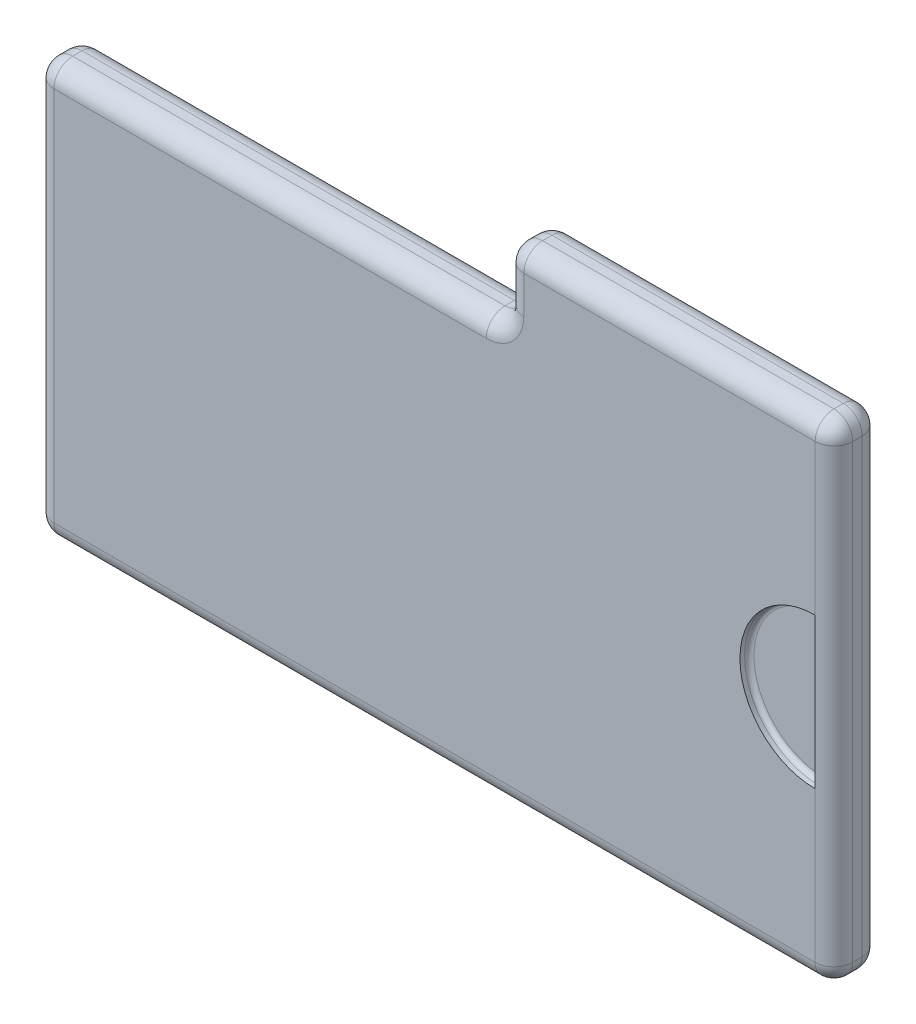
SolidWorks part; units mm, degrees
ref_plane "Alzado" through (0, 0, 0) normal (0, 0, 1) x (1, 0, 0)
ref_plane "Planta" through (0, 0, 0) normal (0, 1, 0) x (1, 0, 0)
ref_plane "Vista lateral" through (0, 0, 0) normal (1, 0, 0) x (0, 0, -1)
sketch "Croquis1" plane through (0, 0, 0) normal (0, 0, 1) x (1, 0, 0)
  line L0 (7.5, 26) -> (42.5, 26)
  line L2 (-42.5, 18) -> (-42.5, -26)
  line L3 (-42.5, -26) -> (42.5, -26)
  line L4 (42.5, 26) -> (42.5, -26)
  line L7 (-7.5, 18) -> (7.5, 18)
  line L8 (7.5, 26) -> (7.5, 18)
  line L9 (-7.5, 18) -> (-42.5, 18)
  point P0 (42.5, 0)
  point P4 (0, 18)
  point P8 (0, -26)
  dimension "D1" = 85
  dimension "D2" = 52
  dimension "D3" = 15
  dimension "D4" = 8
extrude "Saliente-Extruir1" add sketch "Croquis1" along normal mid plane 5
fillet "Redondeo1" radius 2 18 edges at (7.5, 22, 2.5) (7.5, 22, -2.5) (42.5, 0, 2.5) (42.5, 0, -2.5) (42.5, 26, 0) (25, 26, 2.5) (7.5, 26, 0) (25, 26, -2.5) (7.5, 18, 0) (-17.5, 18, 2.5) (-17.5, 18, -2.5) (-42.5, 18, 0) (-42.5, -4, 2.5) (-42.5, -4, -2.5) (-42.5, -26, 0) (0, -26, 2.5) (42.5, -26, 0) (0, -26, -2.5)
sketch "Croquis2" plane through (0, 0, 2.5) normal (0, 0, 1) x (1, 0, 0)
  line L0 (40.5, 8) -> (40.5, -8)
  line L1 (40.5, -24) -> (40.5, 24) construction
  arc A0 (40.5, -8) -> (40.5, 8) centre (40.5, 0) cw
  point P5 (0, 0)
  dimension "D1" = 8
extrude "Cortar-Extruir1" cut sketch "Croquis2" against normal blind 1
fillet "Redondeo2" radius 0.5 2 edges at (40.5, 0, 1.5) (32.5, 0, 1.5)
